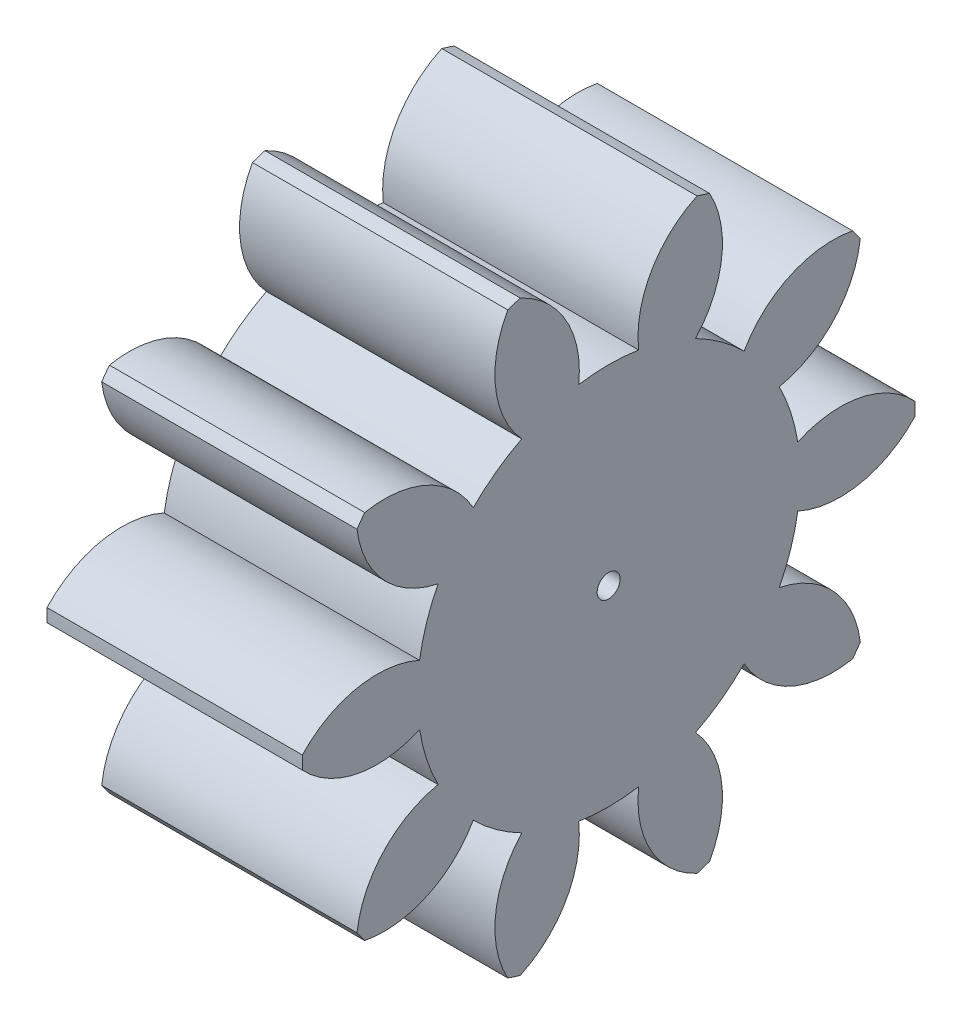
SolidWorks part; units mm, degrees
ref_plane "Plane1" through (0, 0, 0) normal (0, 0, 1) x (1, 0, 0)
ref_plane "Plane2" through (0, 0, 0) normal (0, 1, 0) x (1, 0, 0)
ref_plane "Plane3" through (0, 0, 0) normal (1, 0, 0) x (0, 0, -1)
other "Configuration Table"
sketch "HoldingSke" plane through (0, 0, 0) normal (0, 1, 0) x (1, 0, 0)
  line L0 (0, 0) -> (0.4924, -0.0868)
  line L1 (-15, 0) -> (100, 0) construction
  line L2 (0, 0) -> (-2.1039, 2.3779)
  line L3 (0, 0) -> (-11.863, 4.5341)
  line L4 (0, 0) -> (8.5048, 1.4996)
  line L5 (0, 0) -> (-46.8476, -17.4728)
  line L6 (0, 0) -> (-8.2896, -5.593)
  line L7 (-2.1039, 2.3779) -> (8.6586, 51.2059)
  line L8 (-76.2, 54.61) -> (-76.1, 54.61)
  line L9 (-71.009, 38.7566) -> (-53.1078, 45.2721)
  line L10 (-76.2, 71.12) -> (104.1128, 71.12)
  line L11 (0, 0) -> (-10, 0)
  line L12 (-76.2, 101.6) -> (-76.133, 101.6)
  line L13 (24.9733, 27.94) -> (52.9518, 28.4284)
  line L14 (24.9733, 27.94) -> (24.9743, 27.94)
  line L15 (24.9733, 27.94) -> (100.4006, 29.5858)
  line L16 (-63.627, -2) -> (-12.827, -2)
  circle A0 centre (0, 0) radius 0.45
  circle A1 centre (0, 0) radius 7.499
  circle A2 centre (0, 0) radius 37.5
  circle A3 centre (0, 0) radius 0.45
  dimension "MHD" = 14.998
  dimension "Hub_dia" = 75
  dimension "Bore" = 0.9
  dimension "MBD" = 0.9
  dimension "Num_teeth" = 10
  dimension "Pitch" = 0.5
  dimension "Overall_len" = 50
  dimension "Show_teeth" = 10
  dimension "Thickness" = 10
  dimension "OAL" = 50.0001
  dimension "T_dim" = 0.1
  dimension "Ap" = 20
  dimension "H" = 19.05
  dimension "Pitch_radius" = 180.3128
  dimension "Width" = 10
  dimension "Backlash" = 0.067
  dimension "Addendum_fac" = 1
  dimension "Dedendum_fac" = 1.25
  dimension "Clearance_fac" = 0.25
  dimension "Dedendum_add" = 0.001
  dimension "Module" = 2
sketch "BasProSke" plane through (0, 0, 0) normal (0, 1, 0) x (1, 0, 0)
  line L0 (-10, 0) -> (60, 0) construction
  line L1 (0, 0) -> (0, 12)
  line L2 (0, 0) -> (10, 0)
  line L3 (10, 0) -> (10, 12)
  line L4 (10, 12) -> (0, 12)
  dimension "Thickness" = 10
  dimension "Diameter" = 24
revolve "Base-Revolve" add sketch "BasProSke" angle 360 about L0
sketch "TooCutSke" plane through (0, 0, 0) normal (1, 0, 0) x (0, 0, -1)
  line L1 (0, 0) -> (0, 107) construction
  line L2 (0, 0) -> (-1.6814, 9.8576) construction
  line L3 (0, 0) -> (-6.1153, 18.8209) construction
  line L4 (-1.6814, 9.8576) -> (-3.0576, 9.4105) construction
  arc A0 (1.1737, 7.4066) -> (-1.1737, 7.4066) centre (0, 0) ccw
  arc A1 (3.4979, 11.5054) -> (-3.4979, 11.5054) centre (0, 0) ccw
  circle A2 centre (0, 0) radius 10 construction
  circle A3 centre (0, 0) radius 9.3969 construction
  arc A4 (-1.1737, 7.4066) -> (-3.4979, 11.5054) centre (-5.1477, 7.8615) ccw
  arc A5 (3.4979, 11.5054) -> (1.1737, 7.4066) centre (5.1477, 7.8615) ccw
  dimension "Root_dia" = 14.998
  dimension "Overcut_dia" = 24.0508
  dimension "Pitch_dia" = 20
  dimension "Base_dia" = 18.7939
  dimension "Flank_rad" = 4
  dimension "Half_ang" = 18
  dimension "Half_CT" = 1.4471
extrude "ToothCut" cut sketch "TooCutSke" along normal through all
fillet "Breaks" [suppressed] radius 0.04
fillet "RootFillets" [suppressed] radius 0.501
pattern_circular "TeethCuts" count 10 every 36 about axis through (-10, 0, 0) along (1, 0, 0) of "ToothCut", "RootFillets", "Breaks"
sketch "HubNeaOneSke" plane through (0, 0, 0) normal (-1, 0, 0) x (0, 0, 1)
  circle A0 centre (0, 0) radius 7.499
  dimension "Diameter" = 14.998
extrude "HubNearOne" [suppressed] add sketch "HubNeaOneSke" along normal blind 40.0001
sketch "HubNeaBotSke" plane through (0, 0, 0) normal (-1, 0, 0) x (0, 0, 1)
  circle A0 centre (0, 0) radius 7.499
  dimension "Diameter" = 14.998
extrude "HubNearBoth" [suppressed] add sketch "HubNeaBotSke" along normal blind 20
ref_plane "FarPln" through (10, 0, 0) normal (1, 0, 0) x (0, 0, -1)
sketch "HubFarSke" plane through (10, 0, 0) normal (1, 0, 0) x (0, 0, -1)
  circle A0 centre (0, 0) radius 7.499
  dimension "Diameter" = 14.998
extrude "HubFar" [suppressed] add sketch "HubFarSke" along normal blind 20
sketch "BorSke" plane through (0, 0, 0) normal (1, 0, 0) x (0, 0, -1)
  circle A0 centre (0, 0) radius 0.45
  dimension "Diameter" = 0.9
extrude "Bore" cut sketch "BorSke" along normal mid plane 100.0001
sketch "KeySke" plane through (0, 0, 0) normal (1, 0, 0) x (0, 0, -1)
  line L0 (-0.05, 0) -> (-0.05, 0.55)
  line L1 (-0.05, 0.55) -> (0.05, 0.55)
  line L2 (0.05, 0.55) -> (0.05, 0)
  line L3 (0, 0) -> (0, 34) construction
  line L4 (-0.05, 0) -> (0.05, 0)
  dimension "Offset" = 0.55
  dimension "Width" = 0.1
extrude "Keyway" [suppressed] cut sketch "KeySke" along normal mid plane 100.0001
pattern_circular "Keyway2" [suppressed] count 2 every 90 about axis through (-10, 0, 0) along (1, 0, 0)
equation "' \"Module@HoldingSke\" = 6.35"
equation "' \"Num_teeth@HoldingSke\" = 12"
equation "' \"Ap@HoldingSke\" =  20"
equation "' \"Ap@HoldingSke\" = 20"
equation "' \"Width@HoldingSke\" = 0.5 * 25.4"
equation "' \"Hub_dia@HoldingSke\"= 1 * 25.4"
equation "' \"Hub_dia@HoldingSke\" = 1 * 25.4"
equation "' \"Overall_len@HoldingSke\" = 1.0 * 25.4"
equation "' \"Bore@HoldingSke\" = 0.75 * 25.4"
equation "' \"T_dim@HoldingSke\" = 0.1 * 25.4"
equation "' \"Width@KeySke\" = 0.25 * 25.4"
equation "' \"Show_teeth@HoldingSke\" = 13"
equation "' \"Backlash@HoldingSke\" = 0.009 * 25.4"
equation "' \"Addendum_fac@HoldingSke\" = 1.0"
equation "' \"Dedendum_fac@HoldingSke\" = 1.25"
equation "' \"Dedendum_add@HoldingSke\" = 0.00005 * 25.4"
equation "' \"Clearance_fac@HoldingSke\" = 0.25"
equation "\"Pitch@HoldingSke\" = 1 / \"Module@HoldingSke\""
equation "\"Overcut_dia@TooCutSke\" = (\"Num_teeth@HoldingSke\" + 2 * \"Addendum_fac@HoldingSke\") / \"Pitch@HoldingSke\" + 0.002 * 25.4"
equation "\"Pitch_dia@TooCutSke\" = \"Num_teeth@HoldingSke\" / \"Pitch@HoldingSke\""
equation "\"Base_dia@TooCutSke\" = \"Num_teeth@HoldingSke\" / \"Pitch@HoldingSke\" * cos((\"Ap@HoldingSke\"  * 3.14159265 / 180))"
equation "\"Root_dia@TooCutSke\" = (\"Num_teeth@HoldingSke\" + 2) / \"Pitch@HoldingSke\" - 2 * (\"Addendum_fac@HoldingSke\" + \"Dedendum_fac@HoldingSke\") / \"Pitch@HoldingSke\" - \"Dedendum_add@HoldingSke\" * 2"
equation "\"Half_ang@TooCutSke\" = 180 / \"Num_teeth@HoldingSke\""
equation "\"Half_CT@TooCutSke\" = \"Num_teeth@HoldingSke\" / \"Pitch@HoldingSke\" * sin((3.14159265 / 2 / \"Num_teeth@HoldingSke\")) / 2 - 7 * \"Backlash@HoldingSke\" / 4"
equation "\"Flank_rad@TooCutSke\" = \"Num_teeth@HoldingSke\" / \"Pitch@HoldingSke\" / 5"
equation "\"Radius@RootFillets\" = \"Clearance_fac@HoldingSke\" / \"Pitch@HoldingSke\" + \"Dedendum_add@HoldingSke\""
equation "\"Break_rad@Breaks\" = 0.02 / \"Pitch@HoldingSke\""
equation "\"Thickness@HoldingSke\" = \"Width@HoldingSke\""
equation "\"OAL@HoldingSke\" = \"Thickness@HoldingSke\""
equation "\"MHD@HoldingSke\" = (\"Num_teeth@HoldingSke\" + 2) / \"Pitch@HoldingSke\" - 2 * (\"Addendum_fac@HoldingSke\" + \"Dedendum_fac@HoldingSke\")  / \"Pitch@HoldingSke\" - \"Dedendum_add@HoldingSke\" * 2"
equation "\"MBD@HoldingSke\" = (\"Num_teeth@HoldingSke\" + 2) / \"Pitch@HoldingSke\" - 2 * (\"Addendum_fac@HoldingSke\" + \"Dedendum_fac@HoldingSke\")  / \"Pitch@HoldingSke\" - \"Dedendum_add@HoldingSke\" * 2 - 0.002 * 25.4"
equation "\"MHD@HoldingSke\" = ((sgn( \"MHD@HoldingSke\" - \"Hub_dia@HoldingSke\" )-1)*( \"MHD@HoldingSke\" - \"Hub_dia@HoldingSke\" ))/-2+ \"Hub_dia@HoldingSke\""
equation "\"MBD@HoldingSke\" = ((sgn( \"MBD@HoldingSke\" - \"Bore@HoldingSke\" )-1)*( \"MBD@HoldingSke\" - \"Bore@HoldingSke\" ))/-2+ \"Bore@HoldingSke\""
equation "\"OAL@HoldingSke\" = ((sgn( \"OAL@HoldingSke\" - \"Overall_len@HoldingSke\" )+1)*( \"OAL@HoldingSke\" - \"Overall_len@HoldingSke\" ))/2 + \"Overall_len@HoldingSke\" + 0.000002 * 25.4"
equation "\"Num_teeth@TeethCuts\" = int( \"Show_teeth@HoldingSke\" ) + 1"
equation "\"Num_teeth@TeethCuts\" = ((sgn( \"Num_teeth@TeethCuts\" - \"Num_teeth@HoldingSke\" )-1)*( \"Num_teeth@TeethCuts\" - \"Num_teeth@HoldingSke\" ))/-2+ \"Num_teeth@HoldingSke\""
equation "\"Num_teeth@TeethCuts\" = ((sgn( \"Num_teeth@TeethCuts\" - 2.0)+1)*( \"Num_teeth@TeethCuts\" - 2.0))/2 +2.0"
equation "\"Angle@TeethCuts\" = 360.0 / \"Num_teeth@HoldingSke\""
equation "\"Diameter@BasProSke\" = (\"Num_teeth@HoldingSke\" + 2 * \"Addendum_fac@HoldingSke\") / \"Pitch@HoldingSke\""
equation "\"Thickness@BasProSke\"  = \"Thickness@HoldingSke\""
equation "' \"Fillet_rad@BasProSke\" =  \"Thickness@HoldingSke\" * 0.05"
equation "' \"Fillet_rad@BasProSke\" = \"Thickness@HoldingSke\" * 0.05"
equation "\"MHD@HoldingSke\" = ((sgn( \"MHD@HoldingSke\" - \"Root_dia@TooCutSke\" )-1)*( \"MHD@HoldingSke\" - \"Root_dia@TooCutSke\" ))/-2+ \"Root_dia@TooCutSke\""
equation "\"Diameter@HubNeaOneSke\" = \"MHD@HoldingSke\""
equation "\"Length@HubNearOne\" = \"OAL@HoldingSke\" - \"Thickness@BasProSke\""
equation "\"Diameter@HubNeaBotSke\" = \"MHD@HoldingSke\""
equation "\"Length@HubNearBoth\" = ( \"OAL@HoldingSke\" - \"Thickness@BasProSke\" ) / 2.0"
equation "\"Thickness@FarPln\" = \"Thickness@BasProSke\""
equation "\"Diameter@HubFarSke\" = \"MHD@HoldingSke\""
equation "\"Length@HubFar\" = ( \"OAL@HoldingSke\" - \"Thickness@BasProSke\" ) / 2.0"
equation "\"Diameter@BorSke\" = \"MBD@HoldingSke\""
equation "\"D1@Bore\" = \"OAL@HoldingSke\" * 2.0"
equation "\"D1@Keyway\" = \"OAL@HoldingSke\" * 2.0"
equation "\"Offset@KeySke\" = \"T_dim@HoldingSke\" + \"MBD@HoldingSke\" / 2.0"
